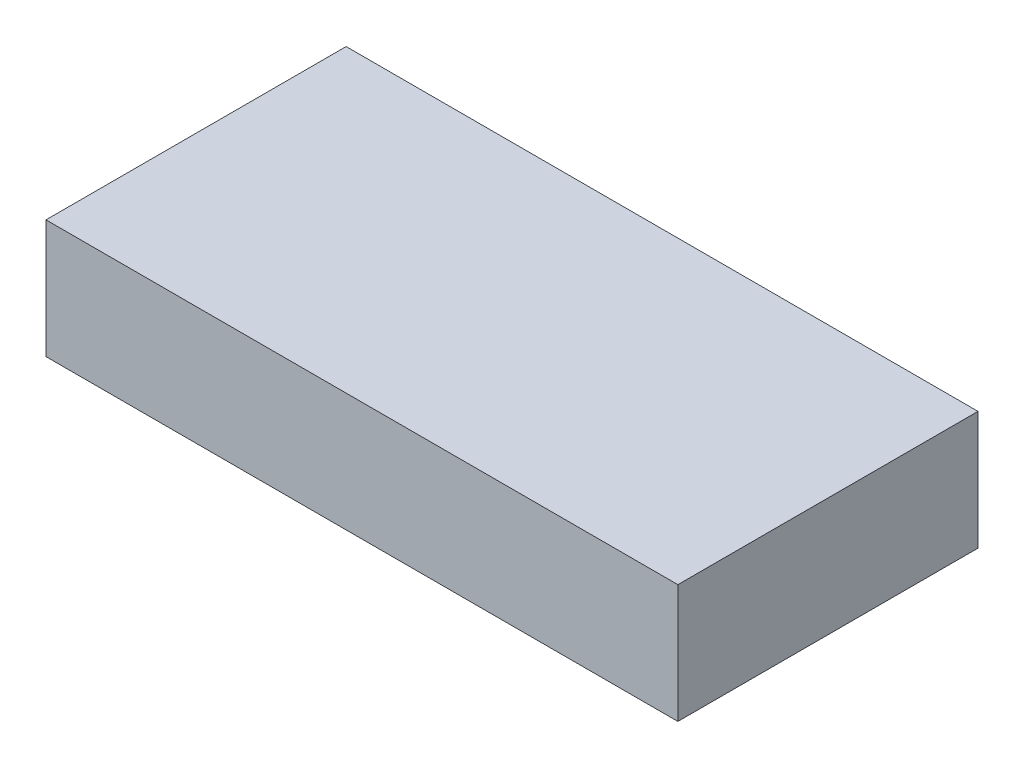
SolidWorks part; units mm, degrees
ref_plane "Front Plane" through (0, 0, 0) normal (0, 0, 1) x (1, 0, 0)
ref_plane "Top Plane" through (0, 0, 0) normal (0, 1, 0) x (1, 0, 0)
ref_plane "Right Plane" through (0, 0, 0) normal (1, 0, 0) x (0, 0, -1)
sketch "Sketch1" plane through (0, 0, 0) normal (0, 1, 0) x (1, 0, 0)
  line L1 (0, 0) -> (-80, 0)
  line L2 (0, 0) -> (0, -38)
  line L3 (0, -38) -> (-80, -38)
  line L4 (-80, 0) -> (-80, -38)
  dimension "D1" = 80
  dimension "D2" = 38
extrude "Boss-Extrude1" add sketch "Sketch1" along normal blind 15
